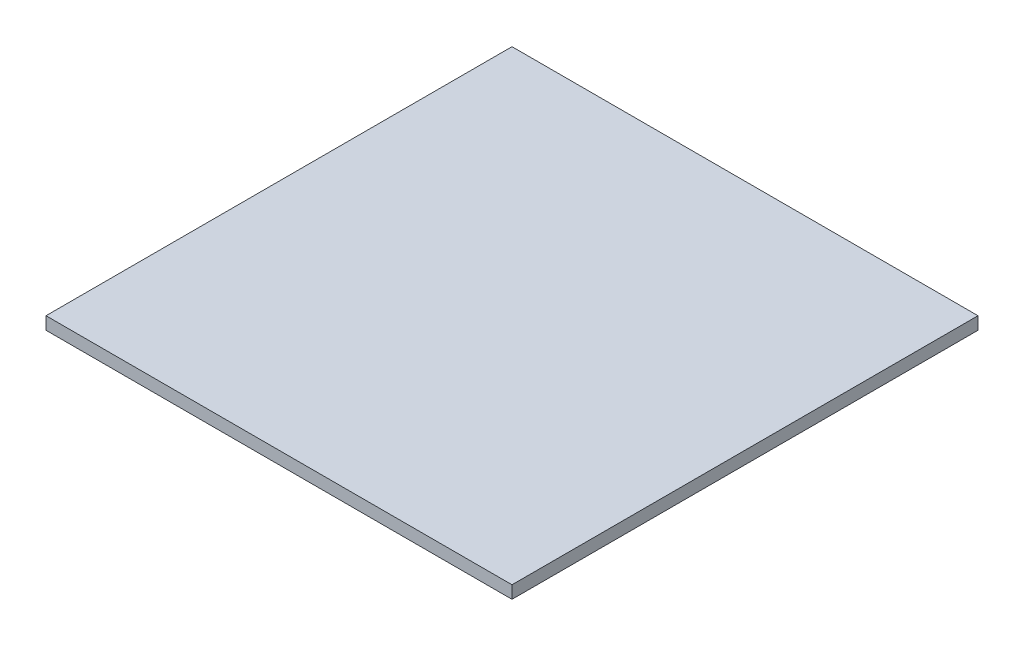
SolidWorks part; units mm, degrees
material "Maple"
ref_plane "Front Plane" through (0, 0, 0) normal (0, 0, 1) x (1, 0, 0)
ref_plane "Top Plane" through (0, 0, 0) normal (0, 1, 0) x (1, 0, 0)
ref_plane "Right Plane" through (0, 0, 0) normal (1, 0, 0) x (0, 0, -1)
sketch "Sketch1" plane through (0, 0, 0) normal (0, 1, 0) x (1, 0, 0)
  line L0 (-95.25, 95.25) -> (95.25, -95.25) construction
  line L1 (-95.25, 95.25) -> (95.25, 95.25)
  line L2 (-95.25, 95.25) -> (-95.25, -95.25)
  line L3 (-95.25, -95.25) -> (95.25, -95.25)
  line L4 (95.25, 95.25) -> (95.25, -95.25)
  dimension "D1" = 190.5
extrude "Boss-Extrude1" add sketch "Sketch1" along normal blind 5.1594
